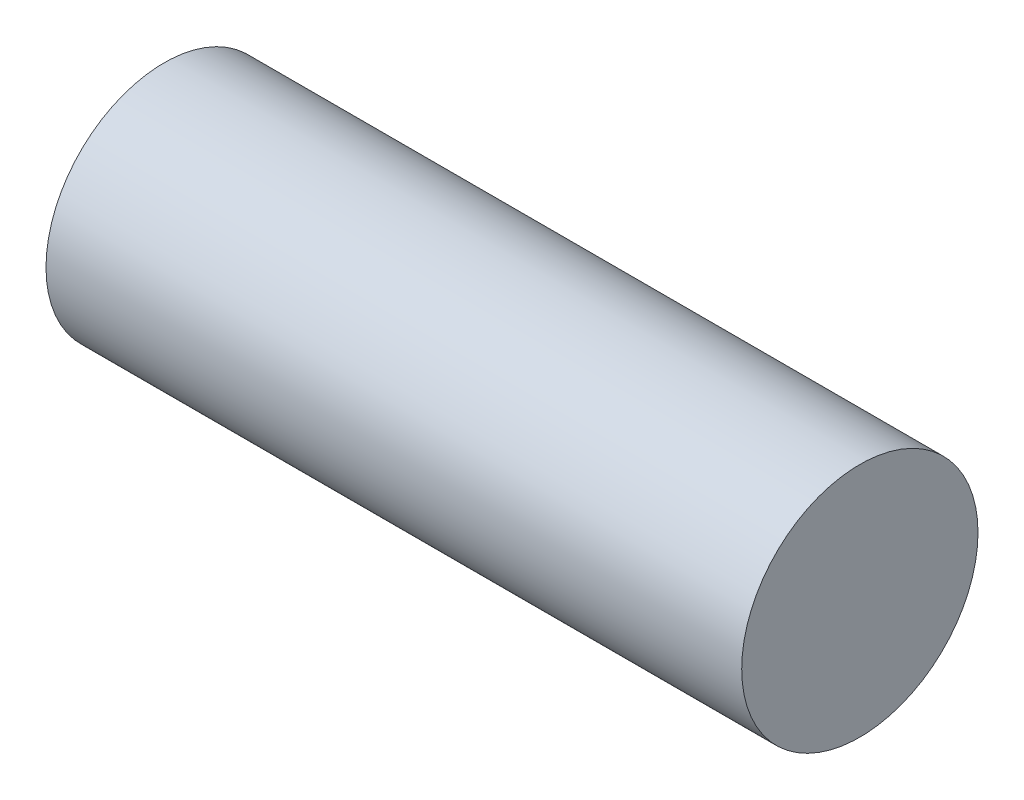
SolidWorks part; units mm, degrees
material "AISI 1045 钢，冷拔"
ref_plane "前视基准面" through (0, 0, 0) normal (0, 0, 1) x (1, 0, 0)
ref_plane "上视基准面" through (0, 0, 0) normal (0, 1, 0) x (1, 0, 0)
ref_plane "右视基准面" through (0, 0, 0) normal (1, 0, 0) x (0, 0, -1)
sketch "草图1" plane through (277.8413, 0, 0) normal (1, 0, 0) x (0, 0, -1)
  circle A0 centre (-1444.0716, -596.4922) radius 12.5673
extrude "凸台-拉伸1" add sketch "草图1" against normal up to surface (74 mm away)
